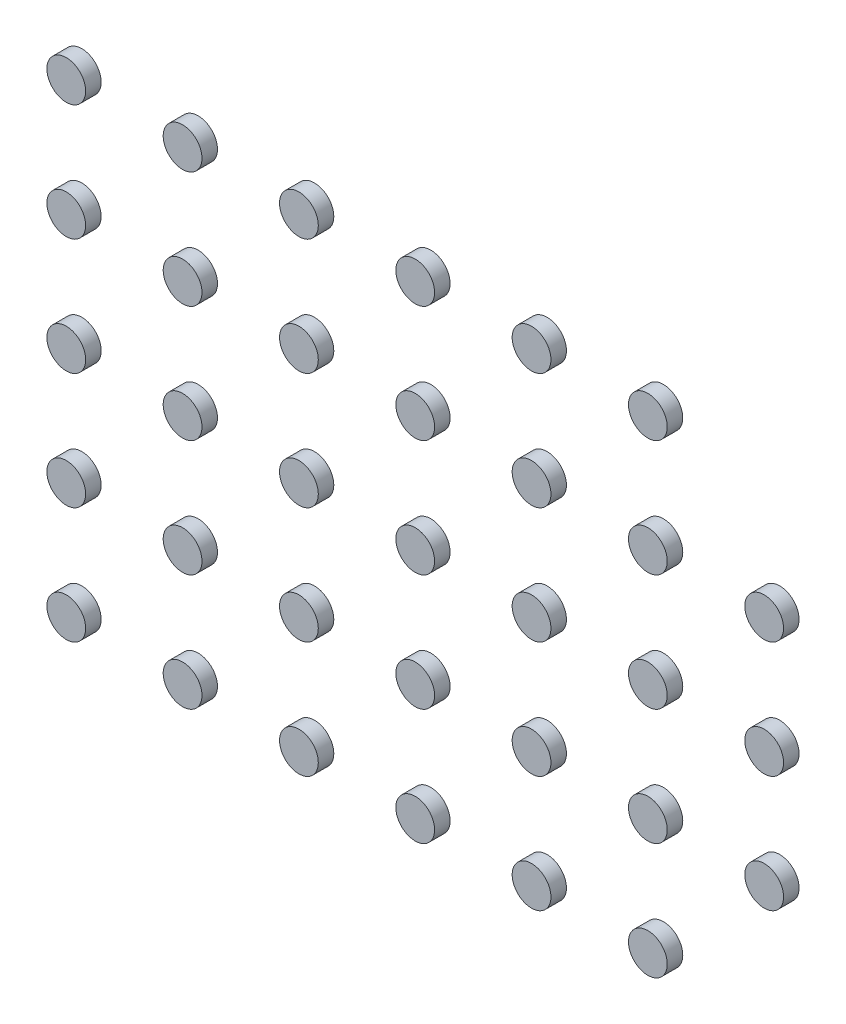
SolidWorks part; units mm, degrees
ref_plane "前视基准面" through (0, 0, 0) normal (0, 0, 1) x (1, 0, 0)
ref_plane "上视基准面" through (0, 0, 0) normal (0, 1, 0) x (1, 0, 0)
ref_plane "右视基准面" through (0, 0, 0) normal (1, 0, 0) x (0, 0, -1)
other "Configuration Table"
sketch "草图1" plane through (0, 0, 0) normal (0, 0, 1) x (1, 0, 0)
  circle A0 centre (-10.5, -7.5) radius 0.5
  circle A1 centre (-10.5, -4.5) radius 0.5
  circle A2 centre (-10.5, -1.5) radius 0.5
  circle A3 centre (-10.5, 4.5) radius 0.5
  circle A4 centre (-7.5, 4.5) radius 0.5
  circle A5 centre (-7.5, -1.5) radius 0.5
  circle A6 centre (-7.5, -4.5) radius 0.5
  circle A7 centre (-7.5, -7.5) radius 0.5
  circle A8 centre (-4.5, -7.5) radius 0.5
  circle A9 centre (-4.5, -4.5) radius 0.5
  circle A10 centre (-4.5, 1.5) radius 0.5
  circle A11 centre (-4.5, 4.5) radius 0.5
  circle A12 centre (-1.5, 4.5) radius 0.5
  circle A13 centre (-1.5, 1.5) radius 0.5
  circle A14 centre (1.5, -1.5) radius 0.5
  circle A15 centre (-1.5, -1.5) radius 0.5
  circle A16 centre (-1.5, -4.5) radius 0.5
  circle A17 centre (-1.5, -7.5) radius 0.5
  circle A18 centre (1.5, -7.5) radius 0.5
  circle A19 centre (1.5, -4.5) radius 0.5
  circle A20 centre (1.5, 1.5) radius 0.5
  circle A21 centre (1.5, 4.5) radius 0.5
  circle A22 centre (4.5, 4.5) radius 0.5
  circle A23 centre (4.5, 1.5) radius 0.5
  circle A24 centre (4.5, -1.5) radius 0.5
  circle A25 centre (4.5, -4.5) radius 0.5
  circle A26 centre (4.5, -7.5) radius 0.5
  circle A27 centre (7.5, -4.5) radius 0.5
  circle A28 centre (7.5, 1.5) radius 0.5
  circle A29 centre (7.5, -1.5) radius 0.5
  circle A30 centre (10.5, -1.5) radius 0.5
  circle A31 centre (10.5, 1.5) radius 0.5
  circle A32 centre (7.5, 4.5) radius 0.5
  circle A33 centre (4.5, 7.5) radius 0.5
  circle A34 centre (1.5, 7.5) radius 0.5
  circle A35 centre (-1.5, 7.5) radius 0.5
  circle A36 centre (-4.5, 7.5) radius 0.5
  circle A37 centre (-7.5, 7.5) radius 0.5
  circle A38 centre (-10.5, 7.5) radius 0.5
  circle A39 centre (-4.5, -1.5) radius 0.5
  circle A40 centre (-1.5, -1.5) radius 0.5
  circle A41 centre (-7.5, 1.5) radius 0.5
  circle A42 centre (-10.5, 1.5) radius 0.5
extrude "凸台-拉伸1" add sketch "草图1" along normal blind 0.4 contours A10 | A13 | A20 | A23 | A28 | A31 | A30 | A29 | A38 | A35 | A34 | A33 | A42 | A3 | A2 | A1 | A0 | A7 | A6 | A5 | A41 | A4 | A11 | A12 | A21 | A32 | A14 | A15 | A39 | A9 | A16 | A8 | A17 | A18 | A26 | A25 | A27 | A24 | A37 | A36 | A22 | A19
delete or keep bodies "实体-删除/保留 1" type keep bodies bodies 143 114 132 147 141 121 130 110 119 128 146 108 117 126 135 144 106 115 124 133 113 131 120 129 109 118 127 136 145 107 116 125 134
